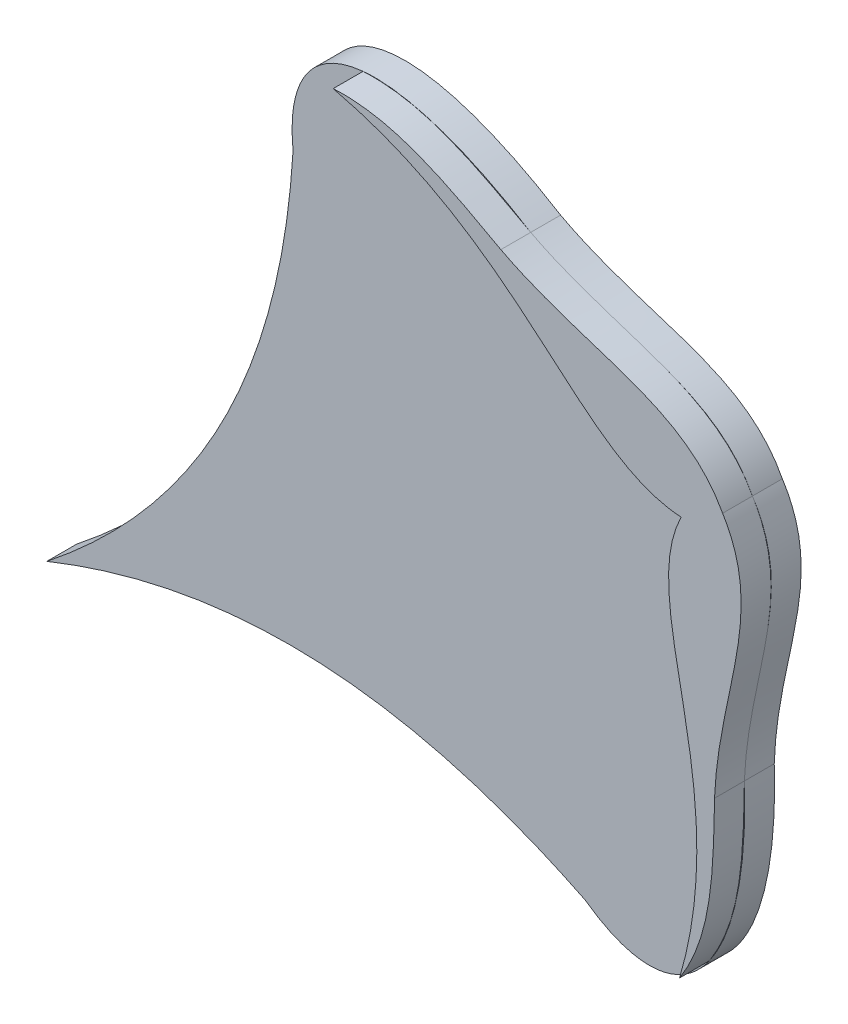
SolidWorks part; units mm, degrees
ref_plane "Front Plane" through (0, 0, 0) normal (0, 0, 1) x (1, 0, 0)
ref_plane "Top Plane" through (0, 0, 0) normal (0, 1, 0) x (1, 0, 0)
ref_plane "Right Plane" through (0, 0, 0) normal (1, 0, 0) x (0, 0, -1)
sketch "Sketch1" plane through (0, 0, 0) normal (0, 0, 1) x (1, 0, 0)
  line L0 (318.6667, 759.5) -> (1593.3333, 759.5) construction
  line L1 (1665.3157, 1173.7868) -> (202.1763, 324.9678) construction
  spline S0 degree 3 poles (1252.9558, 934.5622) (1240.0553, 959.4286) (1208.3652, 958.1395) (1178.692, 973.9033) knots 0 0 0 0 1 1 1 1
  spline S1 degree 3 poles (1178.692, 973.9033) (1128.9788, 1004.5988) (1095.0434, 996.6683) (1099.1114, 957.8662) knots 0 0 0 0 1 1 1 1
  spline S2 degree 3 poles (1099.1114, 957.8662) (1095.4902, 897.8576) (1073.118, 842.1067) (1016.6459, 797.4705) knots 0 0 0 0 1 1 1 1
  spline S3 degree 3 poles (1196.8205, 789.4416) (1142.9292, 816.0852) (1083.4265, 824.3375) (1016.6459, 797.4705) knots 0 0 0 0 1 1 1 1
  spline S4 degree 3 poles (1250.2448, 850.5653) (1252.2148, 792.1724) (1228.4855, 766.6495) (1196.8205, 789.4416) knots 0 0 0 0 1 1 1 1
  spline S5 degree 3 poles (1252.9558, 934.5622) (1268.1388, 911.02) (1251.2893, 884.1496) (1250.2448, 850.5653) knots 0 0 0 0 1 1 1 1
extrude "Boss-Extrude1" add sketch "Sketch1" along normal blind 10
sketch "Sketch2" plane through (0, 0, 10) normal (0, 0, 1) x (1, 0, 0)
  line L0 (1016.6459, 797.4705) -> (1252.9558, 934.5622) construction
  spline S0 degree 3 poles (1239.0469, 926.4932) (1223.6492, 895.0281) (1257.099, 855.7623) (1238.5405, 792.5791) knots 0 0 0 0 1 1 1 1
  spline S1 degree 3 poles (1196.8205, 789.4416) (1228.4855, 766.6495) (1252.2148, 792.1724) (1250.2448, 850.5653) knots 0 0 0 0 1 1 1 1 construction
  spline S2 degree 3 poles (1252.9558, 934.5622) (1267.7895, 910.7984) (1251.5486, 883.5028) (1250.2448, 850.5653) knots 0 0 0 0 1 1 1 1
  spline S3 degree 3 poles (1238.5405, 792.5791) (1249.5429, 809.643) (1249.8536, 828.9508) (1250.2448, 850.5653) knots 0 0 0 0 1 1 1 1
  spline S4 degree 3 poles (1122.5442, 992.5261) (1142.8187, 993.6071) (1159.7342, 984.2928) (1178.692, 973.9033) knots 0 0 0 0 1 1 1 1
  spline S5 degree 3 poles (1252.9558, 934.5622) (1239.6895, 959.2354) (1207.9324, 958.6857) (1178.692, 973.9033) knots 0 0 0 0 1 1 1 1
  spline S6 degree 3 poles (1239.0469, 926.4932) (1204.0888, 928.7451) (1186.6059, 977.2739) (1122.5442, 992.5261) knots 0 0 0 0 1 1 1 1
extrude "Boss-Extrude2" add sketch "Sketch2" along normal blind 10
